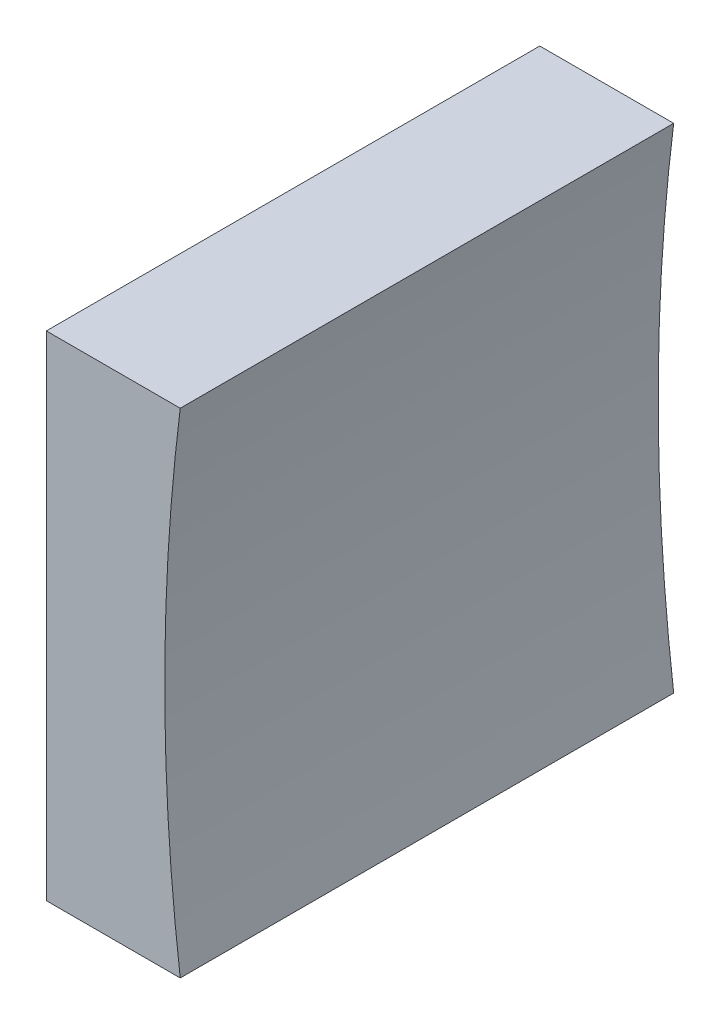
SolidWorks part; units mm, degrees
ref_plane "前视基准面" through (0, 0, 0) normal (0, 0, 1) x (1, 0, 0)
ref_plane "上视基准面" through (0, 0, 0) normal (0, 1, 0) x (1, 0, 0)
ref_plane "右视基准面" through (0, 0, 0) normal (1, 0, 0) x (0, 0, -1)
sketch "草图1" plane through (0, 0, 0) normal (0, 0, 1) x (1, 0, 0)
  line L0 (139.3275, 33.429) -> (149.0915, 33.429) construction
  line L1 (142.3536, 33.429) -> (142.3536, 39.679)
  line L2 (142.3536, 39.679) -> (145.7457, 39.679)
  line L3 (145.7457, 27.179) -> (142.3536, 27.179)
  line L4 (142.3536, 27.179) -> (142.3536, 33.429)
  arc A0 (145.7457, 39.679) -> (145.7457, 27.179) centre (195.3536, 33.429) ccw
  dimension "D1" = 50
  dimension "D2" = 3.3922
extrude "凸台-拉伸1" add sketch "草图1" along normal blind 12.5
